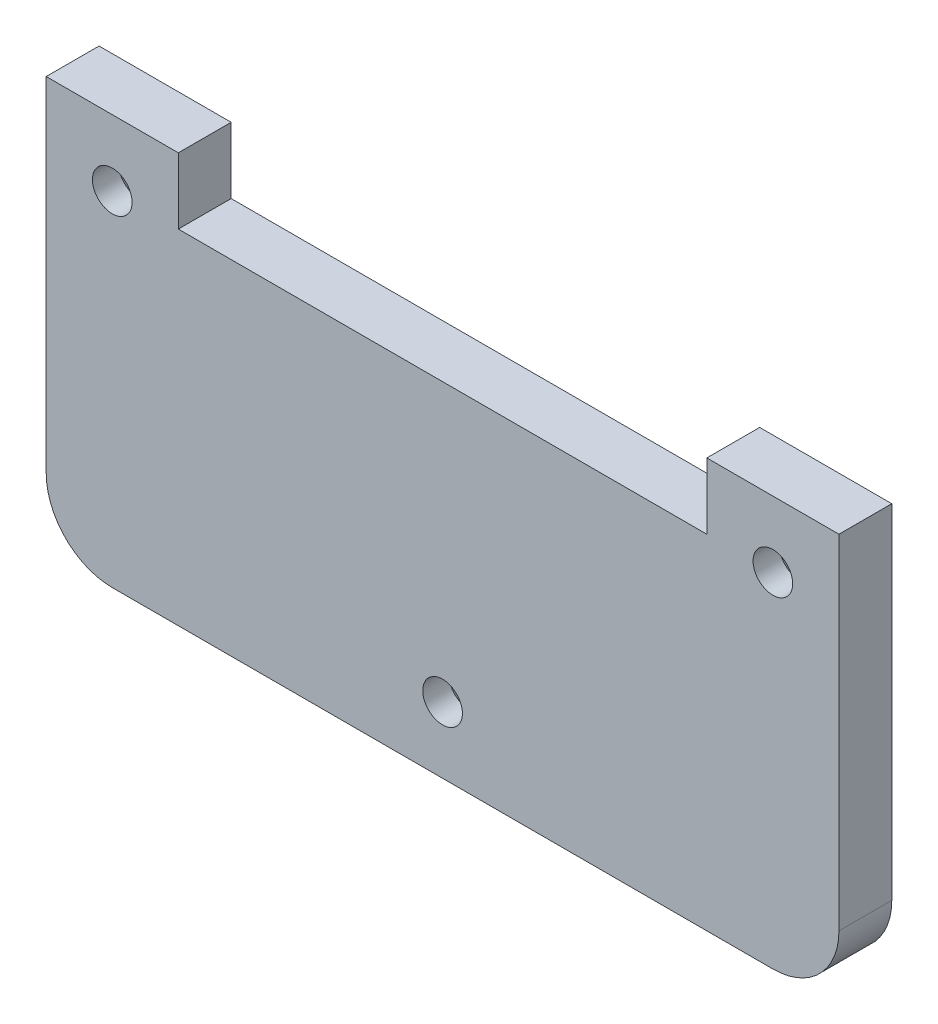
SolidWorks part; units mm, degrees
ref_plane "Plan de face" through (0, 0, 0) normal (0, 0, 1) x (1, 0, 0)
ref_plane "Plan de dessus" through (0, 0, 0) normal (0, 1, 0) x (1, 0, 0)
ref_plane "Plan de droite" through (0, 0, 0) normal (1, 0, 0) x (0, 0, -1)
sketch "Esquisse1" plane through (0, 0, 0) normal (0, 0, 1) x (1, 0, 0)
  line L0 (0, 0) -> (60, 0)
  line L1 (0, 0) -> (0, -26)
  line L2 (60, 0) -> (60, -26)
  line L3 (5, -31) -> (55, -31)
  line L4 (10, 0) -> (50, 0)
  line L5 (10, 0) -> (10, -5)
  line L6 (50, 0) -> (50, -5)
  line L7 (10, -5) -> (50, -5)
  arc A0 (60, -26) -> (55, -31) centre (55, -26) cw
  arc A1 (5, -31) -> (0, -26) centre (5, -26) cw
  point P9 (0, -31)
  dimension "D3" = 5
  dimension "D1" = 60
  dimension "D2" = 31
  dimension "D4" = 10
  dimension "D5" = 10
  dimension "D6" = 5
extrude "Boss.-Extru.1" add sketch "Esquisse1" along normal blind 4 contours A1 L3 A0 L2 L0 L6 L7 L5 L1
sketch "Esquisse2" plane through (0, 0, 4) normal (0, 0, 1) x (1, 0, 0)
  line L0 (0, -21) -> (60, -21) construction
  line L1 (0, 0) -> (0, -26) construction
  line L2 (60, 0) -> (60, -26) construction
  line L3 (30, -21) -> (30, -31) construction
  line L4 (5, -31) -> (55, -31) construction
  line L5 (10, -5) -> (10, -10) construction
  line L6 (10, -10) -> (0, -10) construction
  line L7 (10, -10) -> (0, 0) construction
  circle A0 centre (30, -26) radius 1.5
  circle A1 centre (5, -5) radius 1.5
  circle A2 centre (55, -5) radius 1.5
  dimension "D3" = 3
  dimension "D4" = 3
  dimension "D1" = 5
  dimension "D2" = 10
extrude "Enlèv. mat.-Extru.1" cut sketch "Esquisse2" against normal blind 4
chamfer "Chanfrein1" distance 2 angle 45 3 edges at (6.5, -5, 0) (31.5, -26, 0) (53.5, -5, 0)
